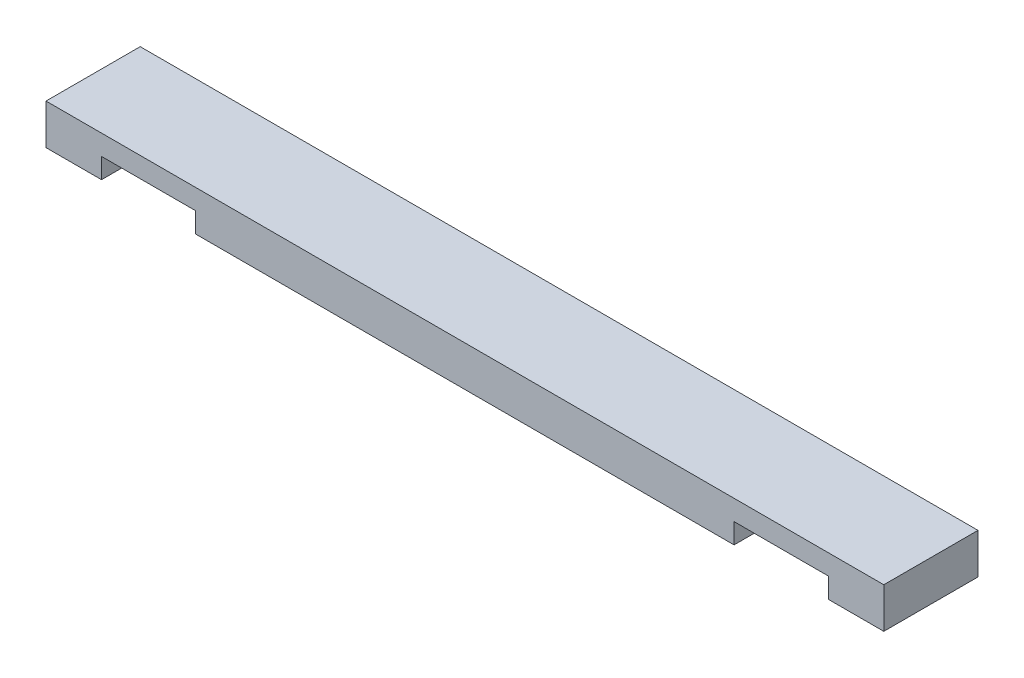
SolidWorks part; units mm, degrees
material "Pine"
ref_plane "Front Plane" through (0, 0, 0) normal (0, 0, 1) x (1, 0, 0)
ref_plane "Top Plane" through (0, 0, 0) normal (0, 1, 0) x (1, 0, 0)
ref_plane "Right Plane" through (0, 0, 0) normal (1, 0, 0) x (0, 0, -1)
sketch "Sketch1" plane through (0, 0, 0) normal (0, 1, 0) x (1, 0, 0)
  line L1 (0, 0) -> (790.575, 0)
  line L2 (0, 0) -> (0, 88.9)
  line L3 (0, 88.9) -> (790.575, 88.9)
  line L4 (790.575, 0) -> (790.575, 88.9)
  dimension "D1" = 88.9
  dimension "D2" = 790.575
extrude "Boss-Extrude1" add sketch "Sketch1" along normal blind 38.1
sketch "Sketch2" plane through (0, 0, 0) normal (0, 0, 1) x (1, 0, 0)
  line L0 (0, 0) -> (790.575, 0) construction
  line L1 (738.1875, 0) -> (649.2875, 0)
  line L2 (738.1875, 0) -> (738.1875, 19.05)
  line L3 (738.1875, 19.05) -> (649.2875, 19.05)
  line L4 (649.2875, 0) -> (649.2875, 19.05)
  line L6 (141.3002, 0) -> (52.4002, 0)
  line L7 (141.3002, 0) -> (141.3002, 19.05)
  line L8 (141.3002, 19.05) -> (52.4002, 19.05)
  line L9 (52.4002, 0) -> (52.4002, 19.05)
  dimension "D1" = 88.9
  dimension "D2" = 19.05
  dimension "D3" = 19.05
  dimension "D4" = 88.9
  dimension "D5" = 52.4002
  dimension "D6" = 649.2875
extrude "Cut-Extrude1" cut sketch "Sketch2" against normal through all
